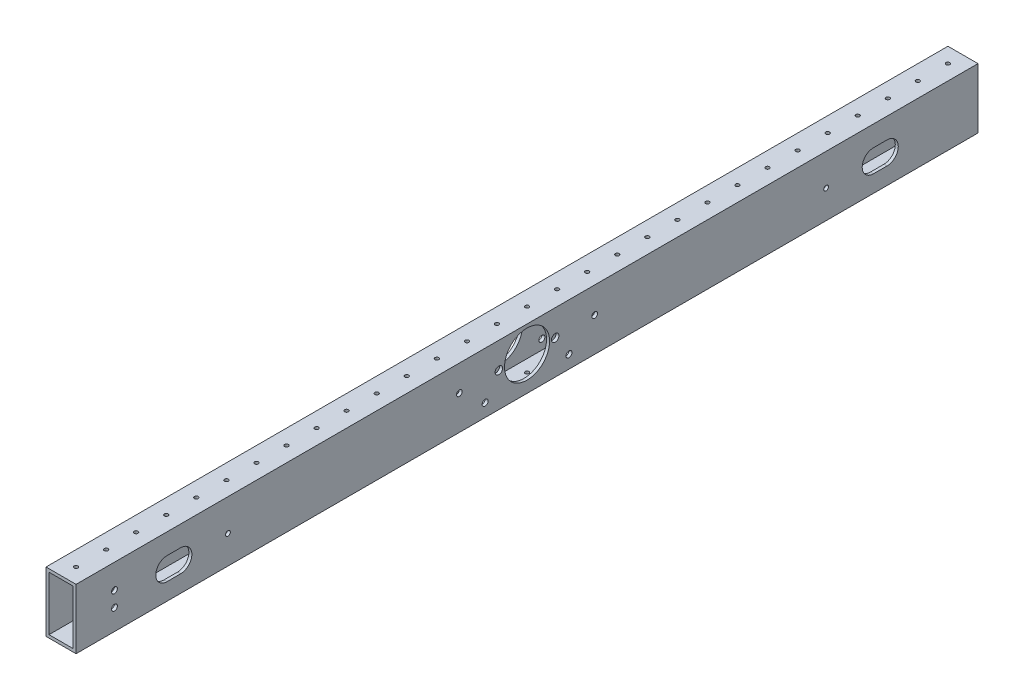
SolidWorks part; units mm, degrees
material "6061-T6 (SS)"
ref_plane "Front Plane" through (0, 0, 0) normal (0, 0, 1) x (1, 0, 0)
ref_plane "Top Plane" through (0, 0, 0) normal (0, 1, 0) x (1, 0, 0)
ref_plane "Right Plane" through (0, 0, 0) normal (1, 0, 0) x (0, 0, -1)
sketch "Sketch1" plane through (0, 0, 0) normal (0, 0, 1) x (1, 0, 0)
  line L1 (0, 0) -> (25.4, 0)
  line L2 (0, 0) -> (0, 50.8)
  line L3 (0, 50.8) -> (25.4, 50.8)
  line L4 (25.4, 0) -> (25.4, 50.8)
  dimension "D1" = 50.8
  dimension "D2" = 25.4
extrude "Extrude-Thin1" add sketch "Sketch1" along normal mid plane 762 thin thin type one direction reverse wall 2.54
sketch "Sketch3" plane through (0, 50.8, 0) normal (0, 1, 0) x (1, 0, 0)
  line L0 (12.7, -381) -> (12.7, -322.109) construction
  line L1 (25.4, -381) -> (0, -381) construction
  circle A0 centre (12.7, -368.3) radius 1.5875
  dimension "D1" = 3.175
  dimension "D2" = 12.7
extrude "Cut-Extrude2" cut sketch "Sketch3" against normal through all
pattern_linear "LPattern1" count 220 spacing 25.4 along (0, 0, -1) of "Cut-Extrude2"
sketch "Sketch6" plane through (25.4, 0, 0) normal (1, 0, 0) x (0, 0, -1)
  line L0 (0, 0) -> (0, 28.7655) construction
  line L7 (-381, 0) -> (381, 0) construction
  line L8 (23.8125, 28.7655) -> (-23.8125, 28.7655) construction
  circle A7 centre (0, 28.7655) radius 19.05
  circle A8 centre (23.8125, 28.7655) radius 3.175
  circle A9 centre (-23.8125, 28.7655) radius 3.175
  point P10 (0, 28.7655)
  dimension "D1" = 28.7655
  dimension "D4" = 23.8125
  dimension "D2" = 38.1
  dimension "D3" = 6.35
extrude "Cut-Extrude5" cut sketch "Sketch6" against normal through all
sketch "Sketch4" plane through (25.4, 0, 0) normal (1, 0, 0) x (0, 0, -1)
  line L0 (292.6945, 23.876) -> (304.1245, 23.876) construction
  line L8 (295.2345, 23.876) -> (0, 28.7655) construction
  line L9 (0, 0) -> (0, 28.7655) construction
  line L11 (-381, 0) -> (381, 0) construction
  line L12 (292.6945, 33.401) -> (304.1245, 33.401)
  line L13 (301.5845, 27.5422) -> (295.2345, 31.2083) construction
  line L14 (295.2345, 31.2083) -> (288.8845, 27.5422) construction
  line L15 (288.8845, 27.5422) -> (288.8845, 20.2098) construction
  line L16 (288.8845, 20.2098) -> (295.2345, 16.5437) construction
  line L17 (295.2345, 16.5437) -> (301.5845, 20.2098) construction
  line L18 (301.5845, 20.2098) -> (301.5845, 27.5422) construction
  line L19 (292.6945, 14.351) -> (304.1245, 14.351)
  line L20 (-381, 0) -> (381, 0) construction
  circle A2 centre (295.2345, 23.876) radius 9.525
  circle A5 centre (295.2345, 23.876) radius 6.35 construction
  circle A6 centre (295.2345, 23.876) radius 6.35 construction
  arc A7 (292.6945, 33.401) -> (292.6945, 14.351) centre (292.6945, 23.876) ccw
  arc A8 (304.1245, 14.351) -> (304.1245, 33.401) centre (304.1245, 23.876) ccw
  point P2 (0, 28.7655)
  point P3 (298.4095, 23.876)
  point P13 (0, 28.7655)
  dimension "D2" = 19.05
  dimension "D3" = 12.7
  dimension "D1" = 23.876
  dimension "D4" = 295.275
  dimension "D5" = 2.54
  dimension "D6" = 8.89
extrude "Cut-Extrude3" cut sketch "Sketch4" against normal through all contours A2 | L19 A8 L12 A2 | L12 A7 L19 A2
mirror "Mirror1" about plane through (0, 0, 0) normal (0, 0, 1) of "Cut-Extrude3"
sketch "Sketch7" plane through (25.4, 0, 0) normal (1, 0, 0) x (0, 0, -1)
  circle A0 centre (57.15, 28.7655) radius 6.35
  circle A1 centre (-57.15, 28.7655) radius 6.35
  dimension "D1" = 12.7
extrude "Cut-Extrude6" cut sketch "Sketch7" against normal up to surface (2.54 mm away) from surface at -22.86 up to face at (0, 25.4, 0) starting at face at (2.54, 23.876, -298.4095)
sketch "Sketch8" plane through (25.4, 0, 0) normal (1, 0, 0) x (0, 0, -1)
  circle A0 centre (-35.4115, 10.9347) radius 2.5273
  circle A1 centre (35.4115, 10.9347) radius 2.5273
  dimension "D1" = 5.0546
extrude "Cut-Extrude7" cut sketch "Sketch8" against normal through all
sketch "Sketch9" plane through (0, 0, 0) normal (-1, 0, 0) x (0, 0, 1)
  line L0 (298.4095, 23.876) -> (252.6895, 23.876) construction
  line L1 (298.4095, 23.876) -> (298.4095, 50.8) construction
  line L2 (381, 50.8) -> (-381, 50.8) construction
  line L4 (292.6945, 33.401) -> (304.1245, 33.401) construction
  line L5 (292.6945, 14.351) -> (304.1245, 14.351) construction
  circle A1 centre (252.6895, 23.876) radius 2.0193
  circle A9 centre (344.1295, 23.876) radius 2.0193 construction
  circle A10 centre (298.4095, 23.876) radius 9.525 construction
  point P16 (298.4095, 33.401)
  dimension "D1" = 4.0386
  dimension "D2" = 45.72
extrude "Cut-Extrude8" cut sketch "Sketch9" against normal through all
mirror "Mirror2" about plane through (0, 0, 0) normal (0, 0, 1) of "Cut-Extrude8"
sketch "Sketch10" plane through (0, 0, 0) normal (-1, 0, 0) x (0, 0, 1)
  circle A0 centre (348.5745, 30.226) radius 2.4892 construction
  circle A1 centre (348.5745, 17.526) radius 2.4892 construction
  circle A2 centre (348.5745, 30.226) radius 2.4892
  circle A3 centre (348.5745, 17.526) radius 2.4892
extrude "Cut-Extrude9" cut sketch "Sketch10" against normal through all
sketch "Sketch11" plane through (0, 0, 0) normal (-1, 0, 0) x (0, 0, 1)
  circle A0 centre (-57.15, 28.7655) radius 2.413
  circle A1 centre (57.15, 28.7655) radius 2.413
  dimension "D1" = 4.826
extrude "Cut-Extrude10" cut sketch "Sketch11" against normal through all
